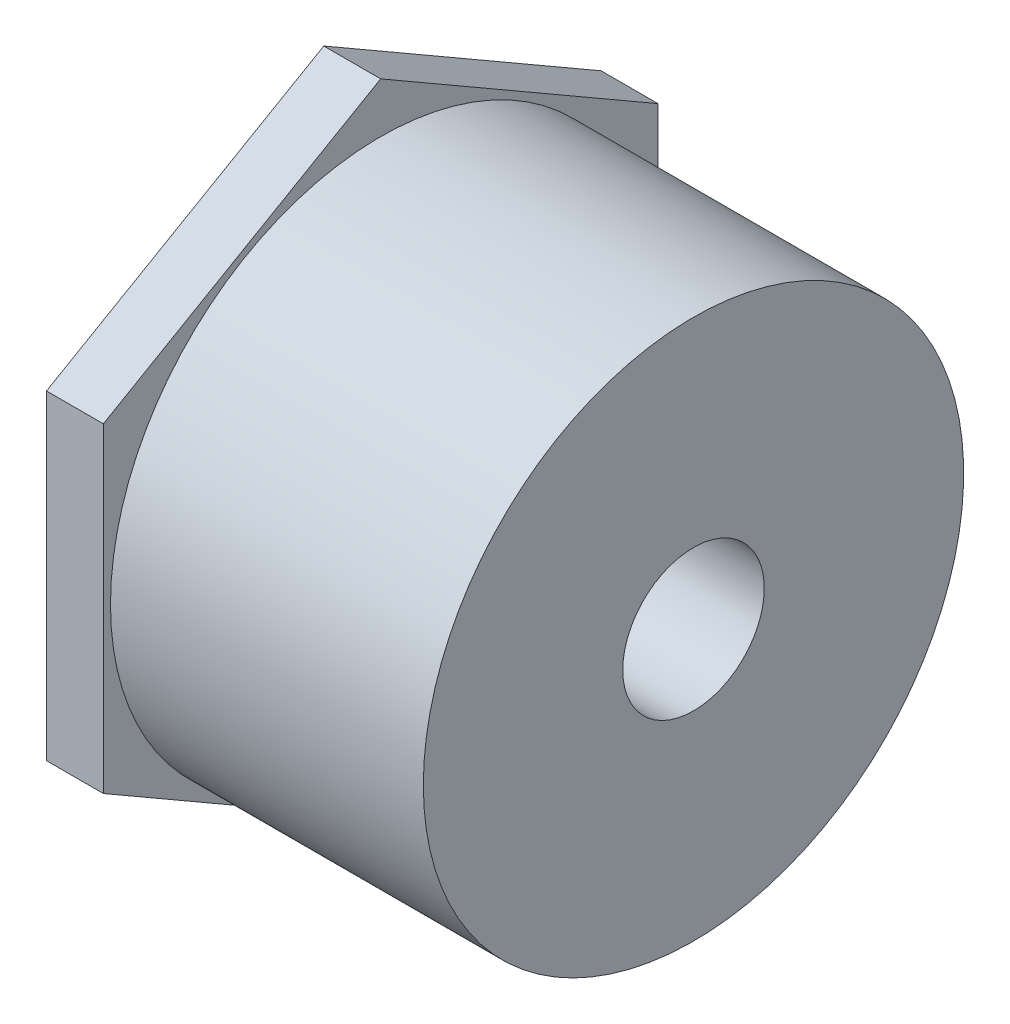
SolidWorks part; units mm, degrees
ref_plane "Front Plane" through (0, 0, 0) normal (0, 0, 1) x (1, 0, 0)
ref_plane "Top Plane" through (0, 0, 0) normal (0, 1, 0) x (1, 0, 0)
ref_plane "Right Plane" through (0, 0, 0) normal (1, 0, 0) x (0, 0, -1)
sketch "Sketch0" plane through (0, 0, 0) normal (0, 0, 1) x (1, 0, 0)
  line L0 (-41.275, 0) -> (0, 0) construction
  line L2 (-29.3624, 30.1625) -> (-29.3624, -30.1625) construction
  line L3 (-34.925, 30.9562) -> (-34.925, -30.9562) construction
  line L5 (-22.225, 10.6172) -> (-41.275, 10.7696) construction
  line L6 (-22.225, 10.6172) -> (-22.225, -10.6172) construction
  line L7 (-22.225, -10.6172) -> (-41.275, -10.7696) construction
  line L8 (-41.275, 10.7696) -> (-41.275, -10.7696) construction
  line L14 (-22.225, 7.8994) -> (-22.225, -7.8994) construction
  line L21 (-41.275, 0) -> (-22.225, 0) construction
  point P12 (-29.3624, 0)
  point P27 (-34.925, 0)
  dimension "A" = 41.275
  dimension "OD A 2" = 21.5392
  dimension "OD B 2" = 21.2344
  dimension "ID 2" = 15.7988
  dimension "B" = 22.225
  dimension "Pipe OD 1" = 60.325
  dimension "C 1" = 29.3624
  dimension "J" = 61.9125
  dimension "K" = 6.35
sketch "Sketch1" plane through (0, 0, 0) normal (0, 0, 1) x (1, 0, 0)
  line L0 (-41.275, 0) -> (0, 0) construction
  line L1 (-41.275, 0) -> (0, 0) construction
  line L2 (-41.275, -30.1625) -> (0, -30.1625)
  line L3 (0, -7.8994) -> (0, -30.1625)
  line L4 (-41.275, -30.1625) -> (-41.275, -10.7696)
  line L5 (-41.275, -10.7696) -> (-22.225, -10.6172)
  line L6 (0, 0) -> (0, -7.8994) construction
  line L8 (-22.225, -7.8994) -> (-22.225, -10.6172)
  line L11 (-22.225, -7.8994) -> (0, -7.8994)
revolve "Revolve1" add sketch "Sketch1" angle 360 about L1
sketch "Sketch2" plane through (-41.275, 0, 0) normal (-1, 0, 0) x (0, 0, 1)
  line L0 (0, 0) -> (0, 35.7452) construction
  line L1 (0, 35.7452) -> (-30.9563, 17.8726)
  line L2 (-30.9563, 17.8726) -> (-30.9563, -17.8726)
  line L3 (-30.9563, -17.8726) -> (0, -35.7452)
  line L4 (0, -35.7452) -> (30.9563, -17.8726)
  line L5 (30.9563, -17.8726) -> (30.9563, 17.8726)
  line L6 (30.9563, 17.8726) -> (0, 35.7452)
  circle A0 centre (0, 0) radius 10.7696 construction
  circle A1 centre (0, 0) radius 10.7696
  circle A2 centre (0, 0) radius 30.9562 construction
  point P3 (0, 30.9562)
extrude "Boss-Extrude1" add sketch "Sketch2" against normal up to vertex (6.35 mm away) up to point (-34.925, 0, 0)
